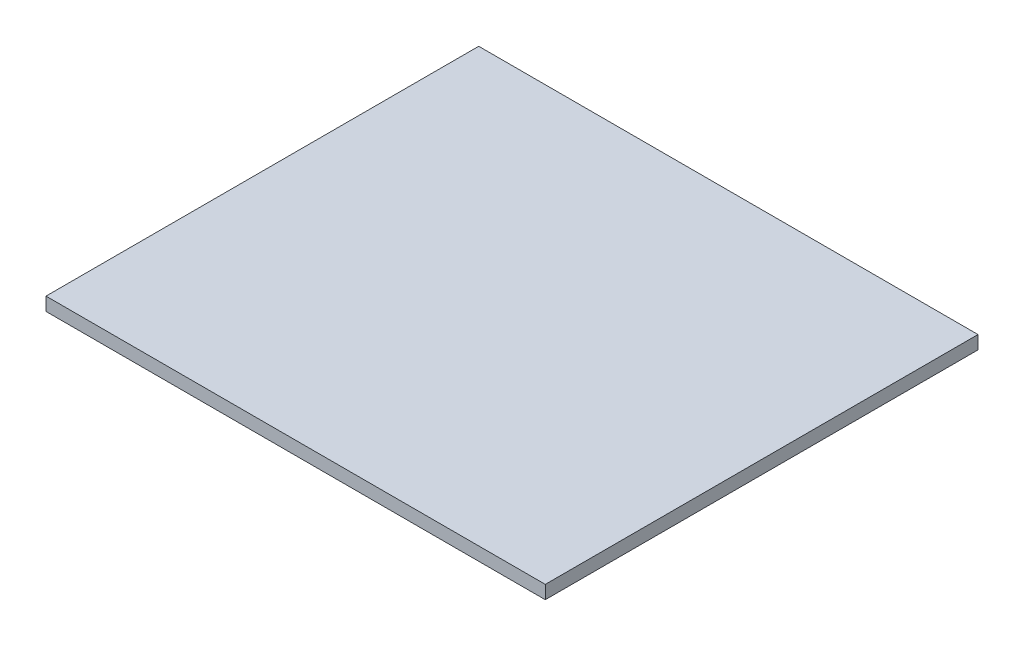
SolidWorks part; units mm, degrees
ref_plane "Front Plane" through (0, 0, 0) normal (0, 0, 1) x (1, 0, 0)
ref_plane "Top Plane" through (0, 0, 0) normal (0, 1, 0) x (1, 0, 0)
ref_plane "Right Plane" through (0, 0, 0) normal (1, 0, 0) x (0, 0, -1)
sketch "Sketch1" plane through (0, 0, 0) normal (0, 1, 0) x (1, 0, 0)
  line L0 (-11.3901, 5.1071) -> (-11.3901, -7.8929)
  line L1 (-11.3901, -7.8929) -> (3.6099, -7.8929)
  line L2 (3.6099, -7.8929) -> (3.6099, 5.1071)
  line L3 (3.6099, 5.1071) -> (-11.3901, 5.1071)
  dimension "D1" = 13
  dimension "15" = 15
extrude "Boss-Extrude1" add sketch "Sketch1" along normal blind 0.4
